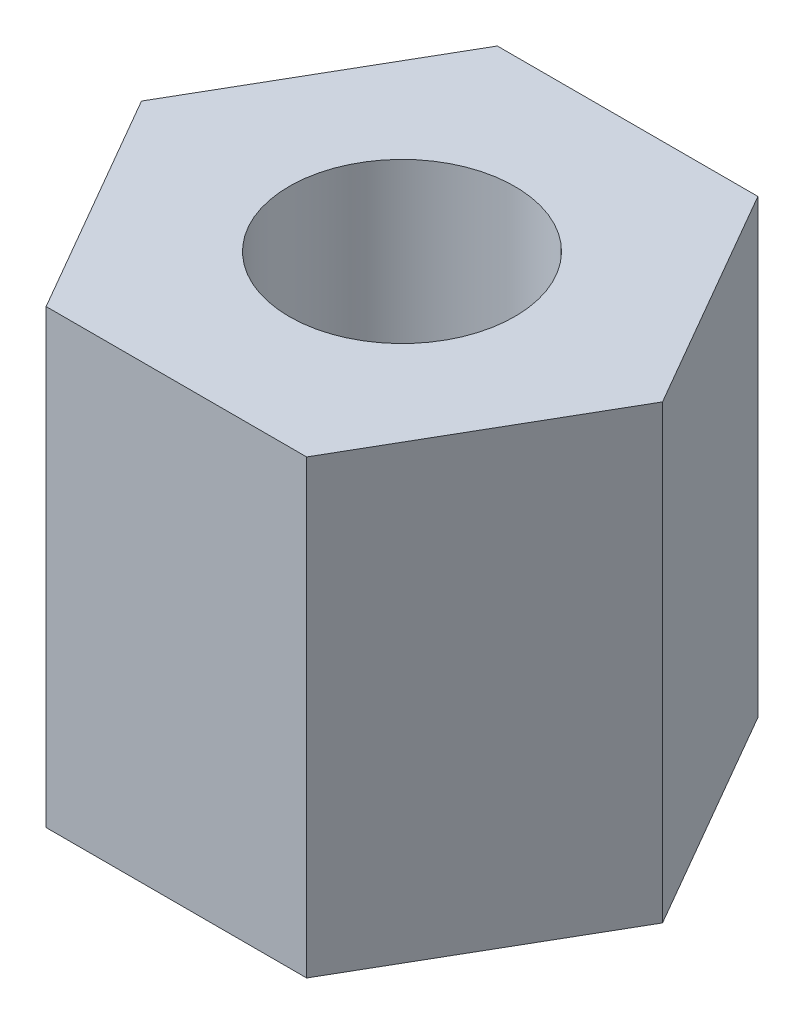
SolidWorks part; units mm, degrees
ref_plane "前视基准面" through (0, 0, 0) normal (0, 0, 1) x (1, 0, 0)
ref_plane "上视基准面" through (0, 0, 0) normal (0, 1, 0) x (1, 0, 0)
ref_plane "右视基准面" through (0, 0, 0) normal (1, 0, 0) x (0, 0, -1)
sketch "草图1" plane through (0, 0, 0) normal (0, 1, 0) x (1, 0, 0)
  line L7 (2.3094, 0) -> (1.1547, 2)
  line L8 (1.1547, 2) -> (-1.1547, 2)
  line L9 (-1.1547, 2) -> (-2.3094, 0)
  line L10 (-2.3094, 0) -> (-1.1547, -2)
  line L11 (-1.1547, -2) -> (1.1547, -2)
  line L12 (1.1547, -2) -> (2.3094, 0)
  circle A0 centre (0, 0) radius 2 construction
  circle A1 centre (0, 0) radius 1
  dimension "D2" = 2
  dimension "D1" = 4
extrude "凸台-拉伸1" add sketch "草图1" along normal blind 4
